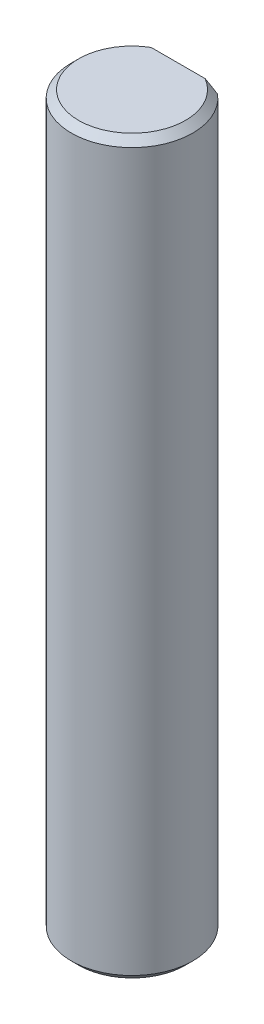
SolidWorks part; units mm, degrees
material "PLA"
ref_plane "Front Plane" through (0, 0, 0) normal (0, 0, 1) x (1, 0, 0)
ref_plane "Top Plane" through (0, 0, 0) normal (0, 1, 0) x (1, 0, 0)
ref_plane "Right Plane" through (0, 0, 0) normal (1, 0, 0) x (0, 0, -1)
sketch "Sketch1" plane through (0, 0, 0) normal (0, 1, 0) x (1, 0, 0)
  circle A0 centre (0, 0) radius 4.15
  dimension "D1" = 8.3
extrude "Boss-Extrude1" add sketch "Sketch1" along normal blind 50
sketch "Sketch2" plane through (0, 50, 0) normal (0, 1, 0) x (1, 0, 0)
  line L0 (-2.7019, 3.15) -> (2.7019, 3.15)
  line L1 (0, 0) -> (0, 4.15) construction
  circle A1 centre (0, 0) radius 4.15
  arc A2 (2.7019, 3.15) -> (-2.7019, 3.15) centre (0, 0) ccw
  point P5 (0, 3.15)
  dimension "D2" = 1
  dimension "D1" = 0
extrude "Cut-Extrude1" cut sketch "Sketch2" against normal blind 16
ref_plane "Plane1" through (0, 25, 0) normal (0, 1, 0) x (1, 0, 0)
mirror "Mirror1" about plane through (0, 25, 0) normal (0, 1, 0) of "Cut-Extrude1"
chamfer "Chamfer1" distance 0.5 angle 45 2 edges at (0, 0, 4.15) (0, 50, 4.15)
